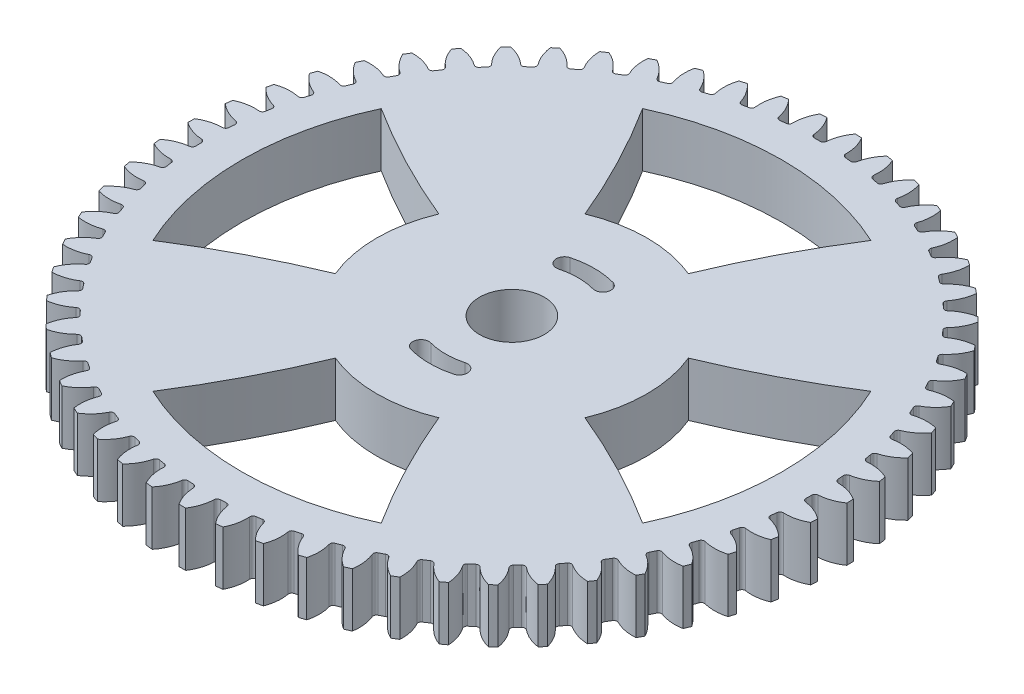
SolidWorks part; units mm, degrees
ref_plane "Plano frontal" through (0, 0, 0) normal (0, 0, 1) x (1, 0, 0)
ref_plane "Plano superior" through (0, 0, 0) normal (0, 1, 0) x (1, 0, 0)
ref_plane "Plano direito" through (0, 0, 0) normal (1, 0, 0) x (0, 0, -1)
sketch "Sketch1" plane through (0, 0, 0) normal (0, 1, 0) x (1, 0, 0)
  circle A0 centre (0, 0) radius 59 construction
  circle A1 centre (0, 0) radius 61
  circle A2 centre (0, 0) radius 56.5
  dimension "D1" = 118
  dimension "D2" = 122
  dimension "D3" = 113
extrude "Boss-Extrude1" add sketch "Sketch1" along normal blind 10 contours A1
sketch "Sketch3" plane through (0, 10, 0) normal (0, 1, 0) x (1, 0, 0)
  line L0 (0, 0) -> (0, 61) construction
  line L1 (-1.5706, 58.9791) -> (1.5706, 58.9791) construction
  line L2 (0, 0) -> (-1.1064, 56.4892) construction
  line L3 (0, 54.6639) -> (-2.6495, 61.9434) construction
  line L4 (0, 0) -> (3.2466, 60.9135) construction
  line L5 (1.5706, 58.9791) -> (4.7074, 58.8119) construction
  circle A0 centre (0, 0) radius 56.5 construction
  circle A1 centre (0, 0) radius 59 construction
  arc A2 (1.1064, 56.4892) -> (-1.1064, 56.4892) centre (0, 0) ccw
  circle A3 centre (0, 0) radius 59 construction
  arc A4 (-3.473, 61.9027) -> (-1.1064, 56.4892) centre (-8.8271, 56.338) cw
  circle A5 centre (0, 0) radius 61 construction
  arc A6 (3.2466, 60.9135) -> (-2.6285, 60.9433) centre (0, 0) ccw
  arc A7 (3.473, 61.9027) -> (1.1064, 56.4892) centre (8.8271, 56.338) ccw
  circle A8 centre (0, 0) radius 62
  arc A9 (3.473, 61.9027) -> (-3.473, 61.9027) centre (0, 0) ccw
  dimension "D2" = 20
  dimension "D3" = 3.051
  dimension "D1" = 1
extrude "Cut-Extrude1" cut sketch "Sketch3" against normal through all contours A7 A6 A4 A2
fillet "Fillet1" radius 0.6 2 edges at (1.1064, 5, -56.4892) (-1.1064, 5, -56.4892)
pattern_circular "CirPattern1" count 59 over 360 about axis through (0, 0, 0) along (0, 1, 0) of "Cut-Extrude1", "Fillet1"
sketch "Sketch4" plane through (0, 10, 0) normal (0, 1, 0) x (1, 0, 0)
  circle A0 centre (0, 0) radius 6
  dimension "D1" = 12
extrude "Cut-Extrude2" cut sketch "Sketch4" against normal up to next
sketch "Sketch5" plane through (0, 10, 0) normal (0, 1, 0) x (1, 0, 0)
  line L0 (0, 0) -> (0, 13.75) construction
  line L1 (0, 0) -> (-3.5588, 13.2815) construction
  line L2 (0, 0) -> (3.5588, 13.2815) construction
  line L3 (-18.9855, 0) -> (14.9361, 0) construction
  arc A1 (-3.947, 14.7304) -> (-3.1705, 11.8326) centre (-3.5588, 13.2815) ccw
  arc A2 (3.947, 14.7304) -> (3.1705, 11.8326) centre (3.5588, 13.2815) cw
  arc A3 (3.1705, 11.8326) -> (-3.1705, 11.8326) centre (0, 0) ccw
  arc A4 (3.947, 14.7304) -> (-3.947, 14.7304) centre (0, 0) ccw
  arc A5 (3.947, -14.7304) -> (-3.947, -14.7304) centre (0, 0) cw
  arc A6 (3.947, -14.7304) -> (3.1705, -11.8326) centre (3.5588, -13.2815) ccw
  arc A7 (3.1705, -11.8326) -> (-3.1705, -11.8326) centre (0, 0) cw
  arc A8 (-3.947, -14.7304) -> (-3.1705, -11.8326) centre (-3.5588, -13.2815) cw
  dimension "D3" = 3
  dimension "D1" = 13.75
  dimension "D2" = 15
extrude "Cut-Extrude3" cut sketch "Sketch5" against normal through all
sketch "Sketch9" plane through (0, 10, 0) normal (0, 1, 0) x (1, 0, 0)
  line L0 (0, 0) -> (0, 50) construction
  line L1 (0, 0) -> (-9.5671, 23.097) construction
  line L2 (0, 0) -> (9.5671, 23.097) construction
  arc A0 (21.1309, 45.3154) -> (-21.1309, 45.3154) centre (0, 0) ccw
  arc A1 (9.5671, 23.097) -> (-9.5671, 23.097) centre (0, 0) ccw
  arc A2 (-21.1309, 45.3154) -> (-9.5671, 23.097) centre (-142.4491, -31.9445) cw
  arc A3 (21.1309, 45.3154) -> (9.5671, 23.097) centre (142.4491, -31.9445) ccw
  arc A4 (23.097, -9.5671) -> (23.097, 9.5671) centre (0, 0) ccw
  arc A5 (45.3154, 21.1309) -> (23.097, 9.5671) centre (-31.9445, 142.4491) cw
  arc A6 (45.3154, -21.1309) -> (45.3154, 21.1309) centre (0, 0) ccw
  arc A7 (45.3154, -21.1309) -> (23.097, -9.5671) centre (-31.9445, -142.4491) ccw
  arc A8 (-9.5671, -23.097) -> (9.5671, -23.097) centre (0, 0) ccw
  arc A9 (21.1309, -45.3154) -> (9.5671, -23.097) centre (142.4491, 31.9445) cw
  arc A10 (-21.1309, -45.3154) -> (21.1309, -45.3154) centre (0, 0) ccw
  arc A11 (-21.1309, -45.3154) -> (-9.5671, -23.097) centre (-142.4491, 31.9445) ccw
  arc A12 (-23.097, 9.5671) -> (-23.097, -9.5671) centre (0, 0) ccw
  arc A13 (-45.3154, -21.1309) -> (-23.097, -9.5671) centre (31.9445, -142.4491) cw
  arc A14 (-45.3154, 21.1309) -> (-45.3154, -21.1309) centre (0, 0) ccw
  arc A15 (-45.3154, 21.1309) -> (-23.097, 9.5671) centre (31.9445, 142.4491) ccw
  point P30 (0, 0)
  dimension "D1" = 100
  dimension "D2" = 50
  dimension "D3" = 45
  dimension "D4" = 50
  dimension "D5" = 4
extrude "Cut-Extrude5" cut sketch "Sketch9" against normal through all
